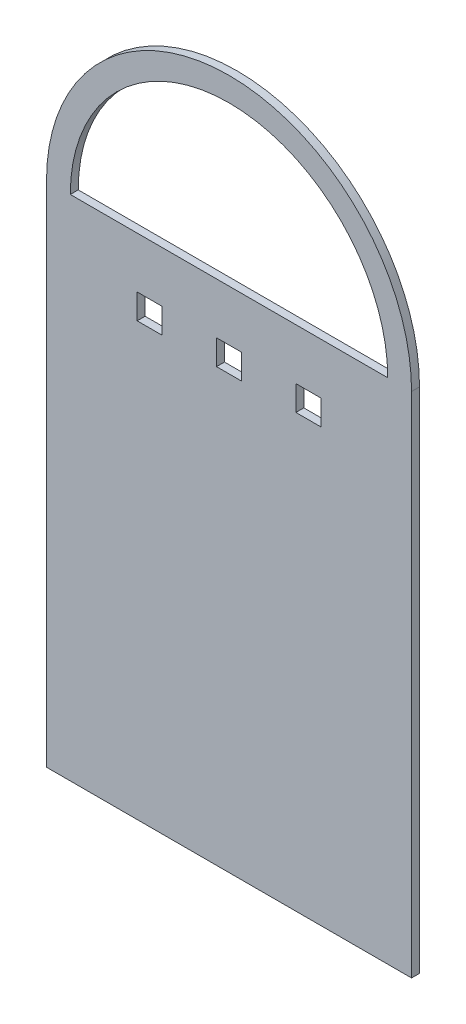
SolidWorks part; units mm, degrees
ref_plane "Front" through (0, 0, 0) normal (0, 0, 1) x (1, 0, 0)
ref_plane "Top" through (0, 0, 0) normal (0, 1, 0) x (1, 0, 0)
ref_plane "Right" through (0, 0, 0) normal (1, 0, 0) x (0, 0, -1)
sketch "Sketch2" plane through (0, 0, 0) normal (0, 0, 1) x (1, 0, 0)
  line L0 (0, 0) -> (146.05, 0)
  line L1 (146.05, 0) -> (146.05, 203.2)
  line L2 (0, 203.2) -> (0, 0)
  line L3 (9.525, 203.2) -> (136.525, 203.2)
  line L4 (41.275, 203.2) -> (41.275, -49796.8) construction
  line L5 (73.025, 203.2) -> (73.025, -49796.8) construction
  line L6 (104.775, 203.2) -> (104.775, -49796.8) construction
  line L7 (40.1195, 177.8) -> (50040.1195, 177.8) construction
  line L9 (36.275, 182.8) -> (46.275, 182.8)
  line L10 (36.275, 182.8) -> (36.275, 172.8)
  line L11 (36.275, 172.8) -> (46.275, 172.8)
  line L12 (46.275, 182.8) -> (46.275, 172.8)
  line L13 (36.275, 182.8) -> (46.275, 172.8) construction
  line L14 (36.275, 172.8) -> (46.275, 182.8) construction
  line L15 (68.025, 182.8) -> (78.025, 182.8)
  line L16 (68.025, 182.8) -> (68.025, 172.8)
  line L17 (68.025, 172.8) -> (78.025, 172.8)
  line L18 (78.025, 182.8) -> (78.025, 172.8)
  line L19 (68.025, 182.8) -> (78.025, 172.8) construction
  line L20 (68.025, 172.8) -> (78.025, 182.8) construction
  line L21 (99.775, 182.8) -> (109.775, 182.8)
  line L22 (99.775, 182.8) -> (99.775, 172.8)
  line L23 (99.775, 172.8) -> (109.775, 172.8)
  line L24 (109.775, 182.8) -> (109.775, 172.8)
  line L25 (99.775, 182.8) -> (109.775, 172.8) construction
  line L26 (99.775, 172.8) -> (109.775, 182.8) construction
  arc A0 (0, 203.2) -> (146.05, 203.2) centre (73.025, 203.2) cw
  arc A1 (9.525, 203.2) -> (136.525, 203.2) centre (73.025, 203.2) cw
  point P9 (73.025, 203.2)
  point P18 (41.275, 177.8)
  point P23 (73.025, 177.8)
  point P28 (104.775, 177.8)
  point P36 (142.7041, 214.0138)
  dimension "D1" = 203.2
  dimension "D2" = 146.05
  dimension "D3" = 127
  dimension "D4" = 25.4
  dimension "D5" = 31.75
  dimension "D6" = 31.75
  dimension "D7" = 10
  dimension "D8" = 10
extrude "Boss-Extrude5" add sketch "Sketch2" along normal blind 3.175
sketch "Sketch4" plane through (0, 0, 3.175) normal (0, 0, 1) x (1, 0, 0)
  line L0 (36.275, 254) -> (36.275, -49746) construction
  line L1 (36.275, 182.8) -> (36.275, 172.8) construction
  line L2 (109.775, 254) -> (109.775, -49746) construction
  line L3 (109.775, 172.8) -> (109.775, 182.8) construction
  text T0 "JuCube" font "Harlow Solid Italic" height 17.78
  point P5 (36.275, 177.8)
  point P10 (109.775, 177.8)
  point P11 (36.275, 121.2416)
  point P12 (36.275, 119.7055)
  point P13 (0, 0)
  point P14 (30.4624, 121.8999)
  point P15 (0, 0)
  point P16 (0, 0)
  point P17 (0, 0)
extrude "Cut-Extrude2" [suppressed] cut sketch "Sketch4" against normal blind 1.5875
